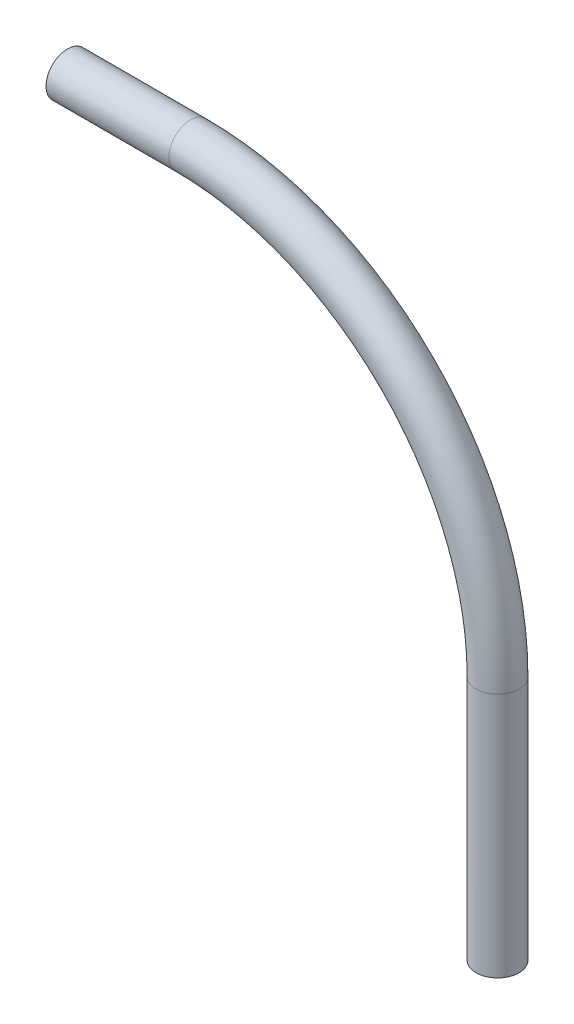
SolidWorks part; units mm, degrees
ref_plane "Ebene vorne" through (0, 0, 0) normal (0, 0, 1) x (1, 0, 0)
ref_plane "Ebene oben" through (0, 0, 0) normal (0, 1, 0) x (1, 0, 0)
ref_plane "Ebene rechts" through (0, 0, 0) normal (1, 0, 0) x (0, 0, -1)
sketch "Skizze1" plane through (0, 0, 0) normal (0, 0, 1) x (1, 0, 0)
  line L0 (0, 0) -> (20, 0)
  line L1 (70, -50) -> (70, -90)
  arc A0 (20, 0) -> (70, -50) centre (20, -50) cw
  dimension "D2" = 50
  dimension "D1" = 20
  dimension "D3" = 40
sketch "Skizze2" plane through (0, 0, 0) normal (1, 0, 0) x (0, 0, -1)
  circle A0 centre (0, 0) radius 3.5
  dimension "D1" = 7
sweep "Austragung1" add profiles "Skizze2" path "Skizze1"
